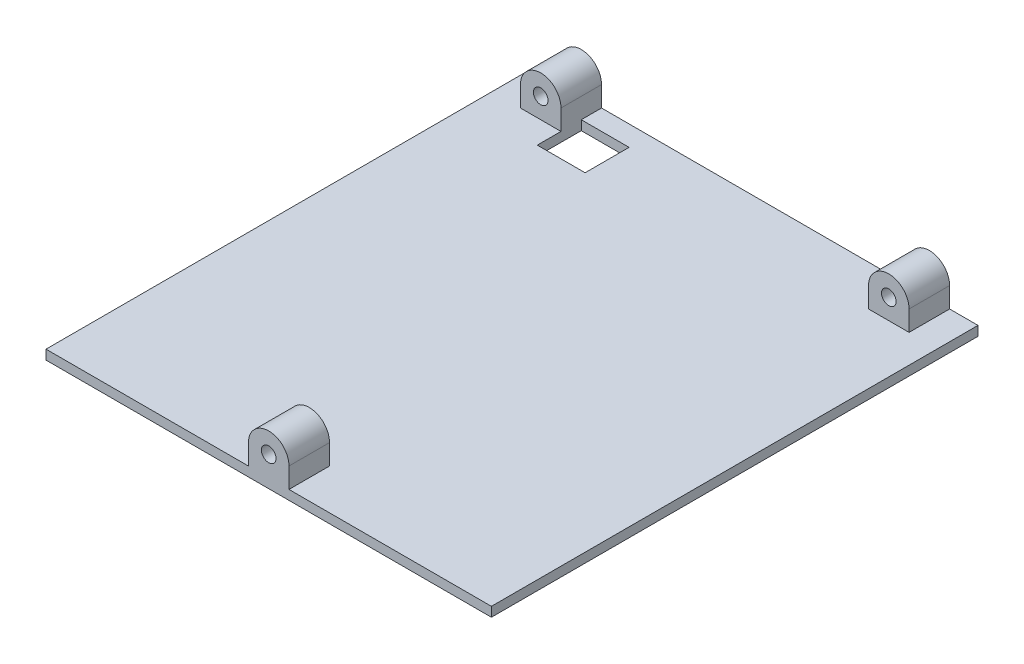
SolidWorks part; units mm, degrees
ref_plane "Front Plane" through (0, 0, 0) normal (0, 0, 1) x (1, 0, 0)
ref_plane "Top Plane" through (0, 0, 0) normal (0, 1, 0) x (1, 0, 0)
ref_plane "Right Plane" through (0, 0, 0) normal (1, 0, 0) x (0, 0, -1)
sketch "Sketch1" plane through (0, 0, 0) normal (0, 1, 0) x (1, 0, 0)
  line L1 (0, 0) -> (139.5, 0)
  line L2 (0, 0) -> (0, 152.4)
  line L3 (0, 152.4) -> (139.5, 152.4)
  line L4 (139.5, 0) -> (139.5, 152.4)
  dimension "D1" = 152.4
  dimension "D2" = 139.5
extrude "Boss-Extrude1" add sketch "Sketch1" along normal blind 6.35
sketch "Sketch2" plane through (0, 6.35, 0) normal (0, 1, 0) x (1, 0, 0)
  line L0 (0, 0) -> (139.5, 0) construction
  line L1 (0, 152.4) -> (139.5, 152.4)
  line L2 (0, 152.4) -> (0, 0)
  line L3 (0, 0) -> (139.5, 0)
  line L4 (139.5, 152.4) -> (139.5, 0)
  line L5 (139.5, 0) -> (139.5, 152.4) construction
extrude "Cut-Extrude1" cut sketch "Sketch2" against normal blind 3.375
sketch "Sketch3" plane through (0, 0, 0) normal (0, 0, 1) x (1, 0, 0)
  line L0 (63.4, 9.325) -> (63.4, 2.975)
  line L1 (63.4, 2.975) -> (76.1, 2.975)
  line L2 (76.1, 9.325) -> (76.1, 2.975)
  line L3 (0, 2.975) -> (139.5, 2.975) construction
  arc A0 (76.1, 9.325) -> (63.4, 9.325) centre (69.75, 9.325) ccw
  circle A1 centre (69.75, 9.325) radius 2.286
  point P6 (69.75, 2.975)
  point P9 (69.75, 2.975)
  dimension "D1" = 4.572
  dimension "D2" = 12.7
  dimension "D8" = 6.35
  dimension "D5" = 6.35
extrude "Boss-Extrude2" add sketch "Sketch3" against normal blind 12.7
sketch "Sketch4" plane through (0, 0, -152.4) normal (0, 0, -1) x (-1, 0, 0)
  line L0 (-130.61, 9.325) -> (-130.61, 2.975)
  line L1 (-130.61, 2.975) -> (-117.91, 2.975)
  line L2 (-117.91, 9.325) -> (-117.91, 2.975)
  line L3 (-21.59, 9.325) -> (-21.59, 2.975)
  line L4 (-21.59, 2.975) -> (-8.89, 2.975)
  line L5 (-8.89, 9.325) -> (-8.89, 2.975)
  line L6 (-139.5, 2.975) -> (0, 2.975) construction
  line L7 (0, 2.975) -> (0, 0) construction
  line L8 (-139.5, 2.975) -> (-139.5, 0) construction
  arc A0 (-117.91, 9.325) -> (-130.61, 9.325) centre (-124.26, 9.325) ccw
  circle A1 centre (-124.26, 9.325) radius 2.286
  arc A2 (-8.89, 9.325) -> (-21.59, 9.325) centre (-15.24, 9.325) ccw
  circle A3 centre (-15.24, 9.325) radius 2.286
  dimension "D1" = 4.572
  dimension "D3" = 6.35
  dimension "D5" = 4.572
  dimension "D7" = 6.35
  dimension "D2" = 6.35
  dimension "D4" = 12.7
  dimension "D6" = 6.35
  dimension "D8" = 12.7
  dimension "D9" = 8.89
  dimension "D10" = 8.89
  dimension "D11" = 15.24
  dimension "D12" = 15.24
extrude "Boss-Extrude3" add sketch "Sketch4" against normal blind 12.7
sketch "Sketch5" plane through (0, 2.975, 0) normal (0, 1, 0) x (1, 0, 0)
  line L0 (21.59, 139.7) -> (21.59, 152.4) construction
  line L1 (21.59, 146.05) -> (36.576, 146.05)
  line L2 (21.59, 146.05) -> (21.59, 132.2705)
  line L3 (21.59, 132.2705) -> (36.576, 132.2705)
  line L4 (36.576, 146.05) -> (36.576, 132.2705)
  line L5 (117.91, 152.4) -> (21.59, 152.4) construction
  dimension "D1" = 13.7795
  dimension "D2" = 14.986
  dimension "D3" = 6.35
extrude "Cut-Extrude2" cut sketch "Sketch5" against normal through all
